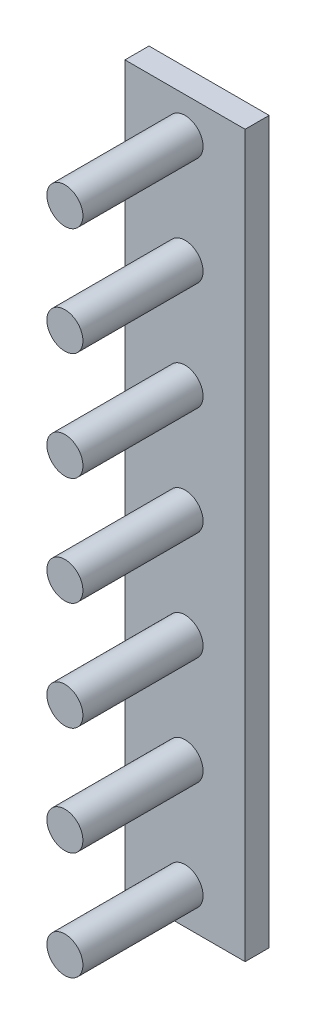
SolidWorks part; units mm, degrees
ref_plane "前视基准面" through (0, 0, 0) normal (0, 0, 1) x (1, 0, 0)
ref_plane "上视基准面" through (0, 0, 0) normal (0, 1, 0) x (1, 0, 0)
ref_plane "右视基准面" through (0, 0, 0) normal (1, 0, 0) x (0, 0, -1)
sketch "草图1" plane through (0, 0, 0) normal (0, 0, 1) x (1, 0, 0)
  line L1 (50, -300) -> (50, 300)
  line L2 (50, -300) -> (-50, -300)
  line L3 (-50, -300) -> (-50, 300)
  line L4 (50, 300) -> (-50, 300)
  line L5 (50, -300) -> (-50, 300) construction
  line L6 (-50, -300) -> (50, 300) construction
  point P0 (0, 0)
  dimension "D1" = 600
  dimension "D2" = 100
extrude "凸台-拉伸1" add sketch "草图1" along normal blind 20
sketch "草图2" plane through (0, 0, 20) normal (0, 0, 1) x (1, 0, 0)
  line L0 (0, -300) -> (0, 300) construction
  line L1 (-50, 0) -> (50, 0) construction
  line L2 (50, 300) -> (-50, 300) construction
  line L3 (-50, -300) -> (50, -300) construction
  line L4 (-50, 300) -> (-50, -300) construction
  line L5 (50, -300) -> (50, 300) construction
  circle A0 centre (0, 0) radius 15
  circle A1 centre (0, 90) radius 15
  circle A2 centre (0, 180) radius 15
  circle A3 centre (0, 270) radius 15
  circle A7 centre (0, -90) radius 15
  circle A8 centre (0, -180) radius 15
  circle A9 centre (0, -270) radius 15
  dimension "D1" = 30
  dimension "D2" = 4
extrude "凸台-拉伸2" add sketch "草图2" along normal blind 100
